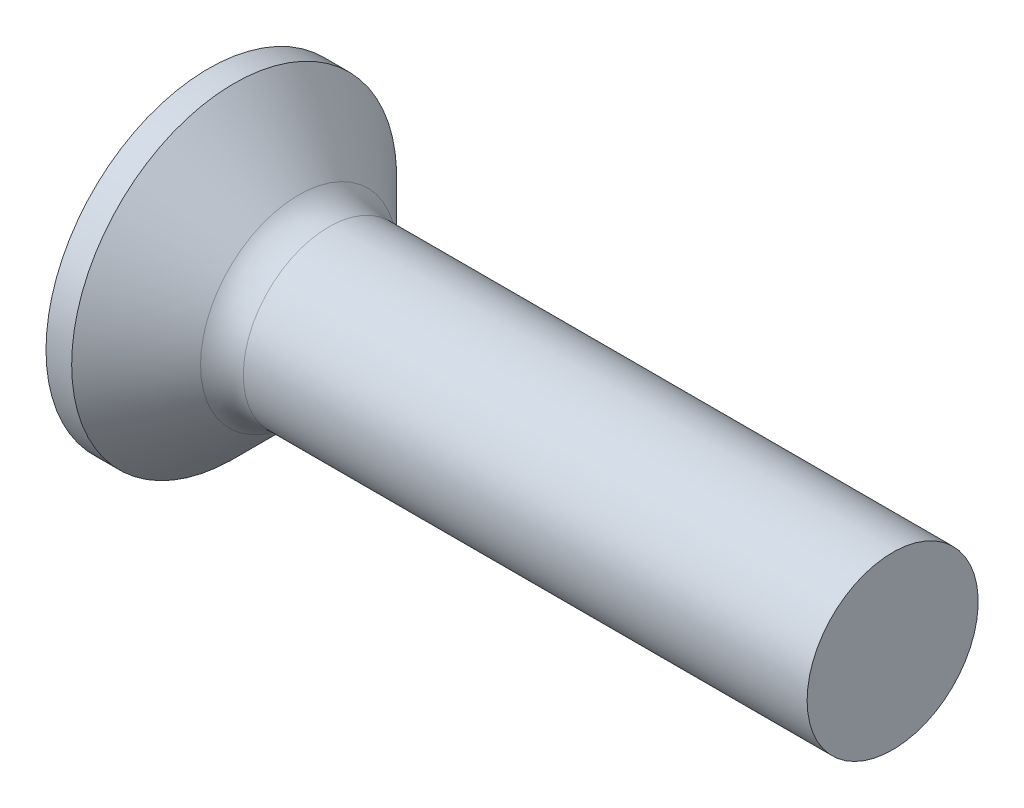
SolidWorks part; units mm, degrees
ref_plane "Plane1" through (0, 0, 0) normal (0, 0, 1) x (1, 0, 0)
ref_plane "Plane2" through (0, 0, 0) normal (0, 1, 0) x (1, 0, 0)
ref_plane "Plane3" through (0, 0, 0) normal (1, 0, 0) x (0, 0, -1)
sketch "BodySke" plane through (0, 0, 0) normal (0, 0, 1) x (1, 0, 0)
  line L0 (0, 0) -> (0, 1.9)
  line L1 (0, 1.9) -> (0.3, 1.9)
  line L2 (1.2, 1) -> (8, 1)
  line L3 (8, 1) -> (8, 0)
  line L4 (8, 0) -> (0, 0)
  line L5 (-6.35, 0) -> (82.55, 0) construction
  line L6 (1.2, -1) -> (8, -1) construction
  line L7 (0.3, -1.9) -> (1.2, -1) construction
  line L8 (0.3, 1.9) -> (1.2, 1)
  line L9 (0, -1.9) -> (0.3, -1.9) construction
  line L10 (1.6, 2.5875) -> (1.6, -6.9375) construction
  line L11 (0, 6.35) -> (0, -3.175) construction
  dimension "Diameter" = 2
  dimension "Length" = 8
  dimension "Head_ht" = 1.2
  dimension "Head_dia" = 3.8
  dimension "Head_ang" = 90
  dimension "D6" = 0.3
  dimension "Advance" = 0.4
  dimension "Thread_nom" = 8
revolve "Base-Revolve" add sketch "BodySke" angle 360 about L5
cosmetic thread "ThreadCosmetic" parameters "Thread_length"=6.4, "Thread_minor"=1.548
fillet "Fillet1" radius 0.5 1 edges at (1.2, 0, 1)
sketch "Sketch3" plane through (0, 0, 0) normal (-1, 0, 0) x (0, 0, 1)
  line L0 (-0.24, 0.95) -> (0.24, 0.95)
  line L1 (0.24, 0.95) -> (0.24, -0.95)
  line L2 (0.24, -0.95) -> (-0.24, -0.95)
  line L3 (-0.24, -0.95) -> (-0.24, 0.95)
  dimension "D1" = 0.95
  dimension "Cross_dia" = 1.9
  dimension "D2" = 0.24
  dimension "Cross_width" = 0.48
ref_plane "Plane4" through (1.2, 0, 0) normal (-1, 0, 0) x (0, 0, 1)
sketch "Sketch4" plane through (1.2, 0, 0) normal (-1, 0, 0) x (0, 0, 1)
  line L0 (-0.24, 0.3517) -> (0.24, 0.3517)
  line L3 (0.24, 0.3517) -> (0.24, -0.3517)
  line L4 (0.24, -0.3517) -> (-0.24, -0.3517)
  line L5 (-0.24, -0.3517) -> (-0.24, 0.3517)
  dimension "D1" = 0.48
  dimension "D2" = 0.7034
  dimension "D3" = 0.24
  dimension "D4" = 0.3517
loft "Recess" cut profiles "Sketch3", "Sketch4"
pattern_circular "RecPat" count 2 every 90 about axis through (0, 0, 0) along (1, 0, 0) of "Recess"
sketch "RecCorSke" plane through (0, 0, 0) normal (0, 0, 1) x (1, 0, 0)
  line L0 (-3.175, 0) -> (15.875, 0) construction
  line L2 (0, 0) -> (0, 0.4394)
  line L3 (0, 0.4394) -> (1.2, 0.3555)
  line L4 (1.2, 0.3555) -> (1.3155, 0)
  line L5 (1.3155, 0) -> (0, 0)
  dimension "Diameter" = 0.711
  dimension "Depth" = 1.2
  dimension "Draft_angle" = 4
  dimension "Bottom_angle" = 18
revolve "RecessCore" cut sketch "RecCorSke" angle 360 about L0
sketch "ThdSchSke" plane through (0, 0, 0) normal (0, 0, 1) x (1, 0, 0)
  line L0 (1.6, -0.774) -> (1.4418, -1)
  line L1 (1.6, -0.774) -> (1.7582, -1)
  line L2 (1.7582, -1) -> (1.7582, -1.25)
  line L3 (-3.175, 0) -> (5.1513, 0) construction
  line L5 (1.7582, -1.25) -> (1.4418, -1.25)
  line L6 (1.4418, -1.25) -> (1.4418, -1)
  line L7 (0, 1.9) -> (0, -1.9) construction
  dimension "Thread_minor" = 1.548
  dimension "Diameter" = 2
  dimension "Start" = 1.6
  dimension "SideAngle" = 55
  dimension "VeeAngle" = 70
  dimension "Overcut" = 2.5
revolve "ThreadSchematic" [suppressed] cut sketch "ThdSchSke" angle 360 about L3
pattern_linear "ThdSchPat" [suppressed]
equation "\"D1@Sketch3\" = \"Cross_dia@Sketch3\" / 2"
equation "\"D2@Sketch3\" = \"Cross_width@Sketch3\" / 2"
equation "\"Depth@RecCorSke\" = \"Cross_depth@Plane4\""
equation "\"D1@Sketch4\" = \"Cross_width@Sketch3\""
equation "\"D2@Sketch4\" = \"Cross_dia@Sketch3\" - 2.0 * \"Cross_depth@Plane4\" * tan(26.5  * 0.017453292)"
equation "\"D3@Sketch4\" = \"D1@Sketch4\" / 2"
equation "\"D4@Sketch4\" = \"D2@Sketch4\" / 2"
equation "\"Thread_length@ThreadCosmetic\" = ((sgn( (\"Length@BodySke\" - \"Advance@BodySke\" * 1.0 - \"Head_ht@BodySke\" ) - \"Thread_nom@BodySke\" )-1)*( (\"Length@BodySke\" - \"Advance@BodySke\" * 1.0 - \"Head_ht@BodySke\" ) - \"Thread_nom@BodySke\" ))/-2+ \"Thread_nom@BodySke\""
equation "\"Thread_minor@ThdSchSke\" = \"Thread_minor@ThreadCosmetic\""
equation "\"Diameter@ThdSchSke\" = \"Diameter@BodySke\""
equation "\"Overcut@ThdSchSke\" = \"Diameter@BodySke\" * 1.25"
equation "\"Start@ThdSchSke\" = 0.000001 + \"Length@BodySke\" - \"Thread_length@ThreadCosmetic\"  '---Countersunk---"
equation "\"Num_threads@ThdSchPat\" = int( \"Thread_length@ThreadCosmetic\" / \"Advance@BodySke\" + 0.999 )  + 1"
equation "\"Advance@ThdSchPat\" = \"Thread_length@ThreadCosmetic\" /  (\"Num_threads@ThdSchPat\" - 1) 'relax it"
